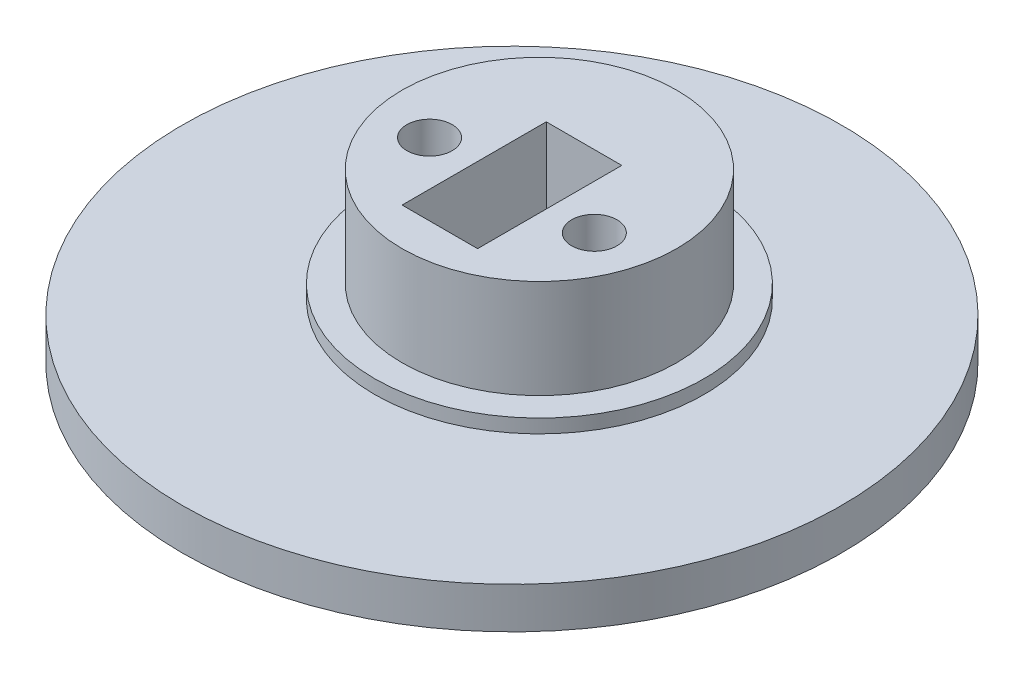
SolidWorks part; units mm, degrees
ref_plane "Front Plane" through (0, 0, 0) normal (0, 0, 1) x (1, 0, 0)
ref_plane "Top Plane" through (0, 0, 0) normal (0, 1, 0) x (1, 0, 0)
ref_plane "Right Plane" through (0, 0, 0) normal (1, 0, 0) x (0, 0, -1)
sketch "Sketch1" plane through (0, 0, 0) normal (0, 1, 0) x (1, 0, 0)
  line L1 (2.75, -5.25) -> (-2.75, -5.25)
  line L2 (2.75, -5.25) -> (2.75, 5.25)
  line L3 (2.75, 5.25) -> (-2.75, 5.25)
  line L4 (-2.75, -5.25) -> (-2.75, 5.25)
  line L5 (2.75, -5.25) -> (-2.75, 5.25) construction
  line L6 (2.75, 5.25) -> (-2.75, -5.25) construction
  circle A0 centre (0, 0) radius 24
  circle A1 centre (-6, 0) radius 1.65
  circle A2 centre (6, 0) radius 1.65
  dimension "D1" = 48
  dimension "D4" = 3.3
  dimension "D2" = 6
  dimension "D3" = 6
  dimension "D5" = 5.5
  dimension "D6" = 10.5
extrude "Boss-Extrude1" add sketch "Sketch1" along normal blind 3
sketch "Sketch2" plane through (0, 3, 0) normal (0, 1, 0) x (1, 0, 0)
  line L0 (-2.75, -5.25) -> (2.75, -5.25) construction
  line L1 (2.75, -5.25) -> (2.75, 5.25) construction
  line L2 (-2.75, 5.25) -> (-2.75, -5.25) construction
  line L3 (2.75, 5.25) -> (-2.75, 5.25) construction
  line L4 (-2.75, -5.25) -> (2.75, -5.25)
  line L5 (2.75, -5.25) -> (2.75, 5.25)
  line L6 (-2.75, 5.25) -> (-2.75, -5.25)
  line L7 (2.75, 5.25) -> (-2.75, 5.25)
  circle A0 centre (0, 2) radius 12
  circle A1 centre (-6, 0) radius 1.65 construction
  circle A2 centre (6, 0) radius 1.65 construction
  circle A3 centre (-6, 0) radius 1.65
  circle A4 centre (6, 0) radius 1.65
  dimension "D2" = 24
  dimension "D1" = 2
extrude "Boss-Extrude2" add sketch "Sketch2" along normal blind 1
sketch "Sketch4" plane through (0, 4, 0) normal (0, 1, 0) x (1, 0, 0)
  line L0 (2.75, -5.25) -> (2.75, 5.25) construction
  line L1 (-2.75, -5.25) -> (2.75, -5.25) construction
  line L2 (-2.75, 5.25) -> (-2.75, -5.25) construction
  line L3 (2.75, 5.25) -> (-2.75, 5.25) construction
  line L4 (2.75, -5.25) -> (2.75, 5.25)
  line L5 (-2.75, -5.25) -> (2.75, -5.25)
  line L6 (-2.75, 5.25) -> (-2.75, -5.25)
  line L7 (2.75, 5.25) -> (-2.75, 5.25)
  circle A0 centre (0, 2) radius 10
  circle A1 centre (-6, 0) radius 1.65 construction
  circle A2 centre (6, 0) radius 1.65 construction
  circle A3 centre (-6, 0) radius 1.65
  circle A4 centre (6, 0) radius 1.65
  dimension "D1" = 20
extrude "Boss-Extrude3" add sketch "Sketch4" along normal blind 7.2
